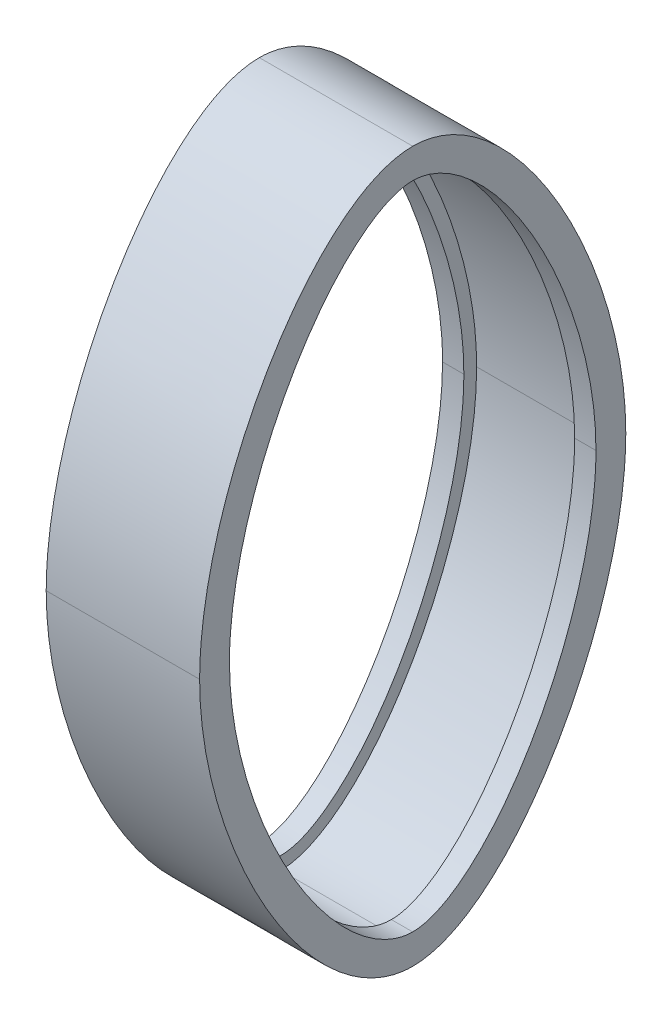
SolidWorks part; units mm, degrees
ref_plane "Front Plane" through (0, 0, 0) normal (0, 0, 1) x (1, 0, 0)
ref_plane "Top Plane" through (0, 0, 0) normal (0, 1, 0) x (1, 0, 0)
ref_plane "Right Plane" through (0, 0, 0) normal (1, 0, 0) x (0, 0, -1)
sketch "Sketch2" plane through (104.3753, 0, 0) normal (1, 0, 0) x (0, 0, -1)
  spline S4 degree 3 poles (2895.0888, -3813.0913) (-3233.4359, 4602.8109) (1881.6451, -5143.077) (-1713.8813, 4640.5368) knots -4.029718 -4.029718 -4.029718 -4.029718 4.699415 4.699415 4.699415 4.699415 only from (-367.1142, -61.0996) to (-317.1142, -144.4329)
  spline S5 degree 3 poles (1079.6132, 4640.4286) (-2515.8324, -5142.9962) (2599.1757, 4602.762) (-3529.3003, -3813.0682) knots -3.699383 -3.699383 -3.699383 -3.699383 5.02971 5.02971 5.02971 5.02971 only from (-317.1142, -144.4329) to (-267.1142, -61.0996)
  spline S6 degree 3 poles (-3529.3171, 3690.8921) (2599.2076, -4725.0101) (-2515.8734, 5020.8778) (1079.653, -4762.736) knots -4.029718 -4.029718 -4.029718 -4.029718 4.699415 4.699415 4.699415 4.699415 only from (-267.1142, -61.0996) to (-317.1142, 22.2337)
  spline S7 degree 3 poles (-1713.8415, -4762.6278) (1881.6041, 5020.797) (-3233.404, -4724.9612) (2895.072, 3690.869) knots -3.699383 -3.699383 -3.699383 -3.699383 5.02971 5.02971 5.02971 5.02971 only from (-317.1142, 22.2337) to (-367.1142, -61.0996)
  spline S8 degree 3 poles (-367.1142, -61.0996) (-367.1142, -97.7663) (-340.4475, -144.4329) (-317.1142, -144.4329) knots 0 0 0 0 1 1 1 1
  spline S9 degree 3 poles (-317.1142, -144.4329) (-293.7808, -144.4329) (-267.1142, -97.7663) (-267.1142, -61.0996) knots 0 0 0 0 1 1 1 1
  spline S10 degree 3 poles (-267.1142, -61.0996) (-267.1142, -24.4329) (-293.7808, 22.2337) (-317.1142, 22.2337) knots 0 0 0 0 1 1 1 1
  spline S11 degree 3 poles (-317.1142, 22.2337) (-340.4475, 22.2337) (-367.1142, -24.4329) (-367.1142, -61.0996) knots 0 0 0 0 1 1 1 1
  dimension "D1" = 0
extrude "Boss-Extrude1" add sketch "Sketch2" along normal offset from surface (18 mm away) 3
sketch "Sketch4" plane through (104.3753, 0, 0) normal (1, 0, 0) x (0, 0, -1)
  spline S8 degree 3 poles (3475.1569, 1041.7378) (-138.7623, 209.0275) (-368.8408, 47.3489) (-359.7286, -68.8551) (-359.5092, -70.7695) (-358.6746, -76.4779) (-357.8851, -80.2373) (-355.9167, -87.6789) (-354.7367, -91.3621) (-352.0035, -98.6494) (-350.4708, -102.1996) (-347.0714, -109.1118) (-345.2056, -112.4743) (-342.112, -117.3521) (-341.0312, -118.9501) (-339.3223, -121.2977) (-338.738, -122.072) (-337.5366, -123.6021) (-336.9186, -124.3591) (-335.0156, -126.5904) (-333.688, -128.0198) (-331.5805, -130.0493) (-330.8585, -130.7065) (-329.3674, -131.9744) (-328.6017, -132.5822) (-327.0312, -133.7267) (-326.2253, -134.2647) (-324.561, -135.2541) (-323.7028, -135.7058) (-321.9148, -136.4905) (-320.9764, -136.8252) (-279.2738, -147.1153) (-205.8613, 18.7108) (533.2817, 3769.6236) knots -3.641992 -3.641992 -3.641992 -3.641992 0.0625 0.0625 0.125 0.125 0.25 0.25 0.375 0.375 0.5 0.5 0.625 0.625 0.6875 0.6875 0.71875 0.71875 0.75 0.75 0.8125 0.8125 0.84375 0.84375 0.875 0.875 0.90625 0.90625 0.9375 0.9375 0.96875 0.96875 2.308967 2.308967 2.308967 2.308967 only from (-360.1142, -61.0996) to (-317.1142, -137.4329)
  spline S9 degree 3 poles (-1217.2008, 3758.4213) (-429.1845, 15.0336) (-354.5726, -146.9888) (-313.7401, -136.946) (-313.2721, -136.8057) (-312.3445, -136.4837) (-311.8854, -136.3021) (-310.5409, -135.7136) (-309.6796, -135.261) (-308.008, -134.2681) (-307.1978, -133.7274) (-306.0131, -132.8637) (-305.6226, -132.5664) (-304.8554, -131.9593) (-304.4785, -131.6495) (-303.3659, -130.7029) (-302.6481, -130.0495) (-300.554, -128.0334) (-299.2364, -126.6159) (-296.7196, -123.6695) (-295.5211, -122.1402) (-293.2233, -118.9884) (-292.1358, -117.3818) (-289.028, -112.4848) (-287.1605, -109.1182) (-283.7648, -102.2154) (-282.2378, -98.6788) (-280.1982, -93.2485) (-279.56, -91.4156) (-278.374, -87.7133) (-277.8294, -85.8538) (-276.3454, -80.2495) (-275.5537, -76.4791) (-274.7182, -70.7628) (-274.4989, -68.8472) (-265.2952, 48.66) (-501.3892, 206.5565) (-4134.1122, 950.7728) knots -1.302809 -1.302809 -1.302809 -1.302809 0.03125 0.03125 0.046875 0.046875 0.0625 0.0625 0.09375 0.09375 0.125 0.125 0.140625 0.140625 0.15625 0.15625 0.1875 0.1875 0.25 0.25 0.3125 0.3125 0.375 0.375 0.5 0.5 0.625 0.625 0.6875 0.6875 0.75 0.75 0.875 0.875 0.9375 0.9375 4.685331 4.685331 4.685331 4.685331 only from (-317.1142, -137.4329) to (-274.1142, -61.0996)
  spline S10 degree 3 poles (-4109.3852, -1163.937) (-495.466, -331.2267) (-265.3875, -169.5481) (-274.4997, -53.3441) (-274.7191, -51.4297) (-275.5537, -45.7213) (-276.3432, -41.9619) (-278.3116, -34.5203) (-279.4916, -30.8371) (-282.2248, -23.5498) (-283.7575, -19.9996) (-287.1569, -13.0874) (-289.0227, -9.7249) (-292.1163, -4.8471) (-293.1971, -3.2491) (-294.906, -0.9015) (-295.4903, -0.1272) (-296.6917, 1.4029) (-297.3097, 2.1599) (-299.2127, 4.3912) (-300.5403, 5.8206) (-302.6478, 7.8501) (-303.3698, 8.5073) (-304.8609, 9.7752) (-305.6266, 10.383) (-307.1971, 11.5275) (-308.003, 12.0655) (-309.6673, 13.0549) (-310.5255, 13.5066) (-312.3135, 14.2913) (-313.252, 14.626) (-354.9545, 24.9161) (-428.367, -140.91) (-1167.51, -3891.8228) knots -3.641992 -3.641992 -3.641992 -3.641992 0.0625 0.0625 0.125 0.125 0.25 0.25 0.375 0.375 0.5 0.5 0.625 0.625 0.6875 0.6875 0.71875 0.71875 0.75 0.75 0.8125 0.8125 0.84375 0.84375 0.875 0.875 0.90625 0.90625 0.9375 0.9375 0.96875 0.96875 2.308967 2.308967 2.308967 2.308967 only from (-274.1142, -61.0996) to (-317.1142, 15.2337)
  spline S11 degree 3 poles (582.9725, -3880.6205) (-205.0438, -137.2328) (-279.6557, 24.7896) (-320.4882, 14.7468) (-320.9562, 14.6065) (-321.8838, 14.2845) (-322.3429, 14.1029) (-323.6874, 13.5144) (-324.5487, 13.0618) (-326.2204, 12.0689) (-327.0305, 11.5282) (-328.2152, 10.6645) (-328.6057, 10.3672) (-329.3729, 9.7601) (-329.7498, 9.4503) (-330.8624, 8.5037) (-331.5802, 7.8503) (-333.6743, 5.8342) (-334.992, 4.4167) (-337.5087, 1.4703) (-338.7073, -0.059) (-341.005, -3.2108) (-342.0925, -4.8174) (-345.2003, -9.7144) (-347.0678, -13.081) (-350.4635, -19.9838) (-351.9905, -23.5204) (-354.0301, -28.9507) (-354.6684, -30.7836) (-355.8543, -34.4859) (-356.399, -36.3454) (-357.8829, -41.9497) (-358.6746, -45.7201) (-359.5101, -51.4364) (-359.7294, -53.352) (-368.9331, -170.8592) (-132.8391, -328.7557) (3499.8839, -1072.972) knots -1.302809 -1.302809 -1.302809 -1.302809 0.03125 0.03125 0.046875 0.046875 0.0625 0.0625 0.09375 0.09375 0.125 0.125 0.140625 0.140625 0.15625 0.15625 0.1875 0.1875 0.25 0.25 0.3125 0.3125 0.375 0.375 0.5 0.5 0.625 0.625 0.6875 0.6875 0.75 0.75 0.875 0.875 0.9375 0.9375 4.685331 4.685331 4.685331 4.685331 only from (-317.1142, 15.2337) to (-360.1142, -61.0996)
  spline S12 degree 3 poles (-360.1142, -61.0996) (-360.1142, -63.0576) (-360.031, -64.9991) (-359.7286, -68.8551) (-359.5092, -70.7695) (-358.6746, -76.4779) (-357.8851, -80.2373) (-355.9167, -87.6789) (-354.7367, -91.3621) (-352.0035, -98.6494) (-350.4708, -102.1996) (-347.0714, -109.1118) (-345.2056, -112.4743) (-342.112, -117.3521) (-341.0312, -118.9501) (-339.3223, -121.2977) (-338.738, -122.072) (-337.5366, -123.6021) (-336.9186, -124.3591) (-335.0156, -126.5904) (-333.688, -128.0198) (-331.5805, -130.0493) (-330.8585, -130.7065) (-329.3674, -131.9744) (-328.6017, -132.5822) (-327.0312, -133.7267) (-326.2253, -134.2647) (-324.561, -135.2541) (-323.7028, -135.7058) (-321.9148, -136.4905) (-320.9764, -136.8252) (-319.0759, -137.2941) (-318.1079, -137.4329) (-317.1142, -137.4329) knots 0 0 0 0 0.0625 0.0625 0.125 0.125 0.25 0.25 0.375 0.375 0.5 0.5 0.625 0.625 0.6875 0.6875 0.71875 0.71875 0.75 0.75 0.8125 0.8125 0.84375 0.84375 0.875 0.875 0.90625 0.90625 0.9375 0.9375 0.96875 0.96875 1 1 1 1
  spline S13 degree 3 poles (-317.1142, -137.4329) (-316.1224, -137.4329) (-315.1582, -137.2948) (-313.7401, -136.946) (-313.2721, -136.8057) (-312.3445, -136.4837) (-311.8854, -136.3021) (-310.5409, -135.7136) (-309.6796, -135.261) (-308.008, -134.2681) (-307.1978, -133.7274) (-306.0131, -132.8637) (-305.6226, -132.5664) (-304.8554, -131.9593) (-304.4785, -131.6495) (-303.3659, -130.7029) (-302.6481, -130.0495) (-300.554, -128.0334) (-299.2364, -126.6159) (-296.7196, -123.6695) (-295.5211, -122.1402) (-293.2233, -118.9884) (-292.1358, -117.3818) (-289.028, -112.4848) (-287.1605, -109.1182) (-283.7648, -102.2154) (-282.2378, -98.6788) (-280.1982, -93.2485) (-279.56, -91.4156) (-278.374, -87.7133) (-277.8294, -85.8538) (-276.3454, -80.2495) (-275.5537, -76.4791) (-274.7182, -70.7628) (-274.4989, -68.8472) (-274.1969, -64.9923) (-274.1142, -63.0531) (-274.1142, -61.0996) knots 0 0 0 0 0.03125 0.03125 0.046875 0.046875 0.0625 0.0625 0.09375 0.09375 0.125 0.125 0.140625 0.140625 0.15625 0.15625 0.1875 0.1875 0.25 0.25 0.3125 0.3125 0.375 0.375 0.5 0.5 0.625 0.625 0.6875 0.6875 0.75 0.75 0.875 0.875 0.9375 0.9375 1 1 1 1
  spline S14 degree 3 poles (-274.1142, -61.0996) (-274.1142, -59.1416) (-274.1973, -57.2001) (-274.4997, -53.3441) (-274.7191, -51.4297) (-275.5537, -45.7213) (-276.3432, -41.9619) (-278.3116, -34.5203) (-279.4916, -30.8371) (-282.2248, -23.5498) (-283.7575, -19.9996) (-287.1569, -13.0874) (-289.0227, -9.7249) (-292.1163, -4.8471) (-293.1971, -3.2491) (-294.906, -0.9015) (-295.4903, -0.1272) (-296.6917, 1.4029) (-297.3097, 2.1599) (-299.2127, 4.3912) (-300.5403, 5.8206) (-302.6478, 7.8501) (-303.3698, 8.5073) (-304.8609, 9.7752) (-305.6266, 10.383) (-307.1971, 11.5275) (-308.003, 12.0655) (-309.6673, 13.0549) (-310.5255, 13.5066) (-312.3135, 14.2913) (-313.252, 14.626) (-315.1524, 15.0949) (-316.1204, 15.2337) (-317.1142, 15.2337) knots 0 0 0 0 0.0625 0.0625 0.125 0.125 0.25 0.25 0.375 0.375 0.5 0.5 0.625 0.625 0.6875 0.6875 0.71875 0.71875 0.75 0.75 0.8125 0.8125 0.84375 0.84375 0.875 0.875 0.90625 0.90625 0.9375 0.9375 0.96875 0.96875 1 1 1 1
  spline S15 degree 3 poles (-317.1142, 15.2337) (-318.1059, 15.2337) (-319.0701, 15.0956) (-320.4882, 14.7468) (-320.9562, 14.6065) (-321.8838, 14.2845) (-322.3429, 14.1029) (-323.6874, 13.5144) (-324.5487, 13.0618) (-326.2204, 12.0689) (-327.0305, 11.5282) (-328.2152, 10.6645) (-328.6057, 10.3672) (-329.3729, 9.7601) (-329.7498, 9.4503) (-330.8624, 8.5037) (-331.5802, 7.8503) (-333.6743, 5.8342) (-334.992, 4.4167) (-337.5087, 1.4703) (-338.7073, -0.059) (-341.005, -3.2108) (-342.0925, -4.8174) (-345.2003, -9.7144) (-347.0678, -13.081) (-350.4635, -19.9838) (-351.9905, -23.5204) (-354.0301, -28.9507) (-354.6684, -30.7836) (-355.8543, -34.4859) (-356.399, -36.3454) (-357.8829, -41.9497) (-358.6746, -45.7201) (-359.5101, -51.4364) (-359.7294, -53.352) (-360.0314, -57.2069) (-360.1142, -59.1461) (-360.1142, -61.0996) knots 0 0 0 0 0.03125 0.03125 0.046875 0.046875 0.0625 0.0625 0.09375 0.09375 0.125 0.125 0.140625 0.140625 0.15625 0.15625 0.1875 0.1875 0.25 0.25 0.3125 0.3125 0.375 0.375 0.5 0.5 0.625 0.625 0.6875 0.6875 0.75 0.75 0.875 0.875 0.9375 0.9375 1 1 1 1
  dimension "D1" = 7
extrude "Cut-Extrude2" cut sketch "Sketch4" along normal up to surface (5 mm away)
sketch "Sketch6" plane through (109.3753, 0, 0) normal (-1, 0, 0) x (0, 0, 1)
  spline S0 degree 3 poles (-321.1313, 2789.2693) (198.4498, 26.5186) (275.2056, -149.6018) (320.6862, -139.9947) (321.185, -139.865) (322.1755, -139.5638) (322.6663, -139.3923) (324.1036, -138.8318) (325.025, -138.3949) (326.8125, -137.4263) (327.6785, -136.8944) (329.3659, -135.7541) (330.1872, -135.1456) (331.7925, -133.8643) (332.5735, -133.1936) (334.8449, -131.121) (336.2725, -129.653) (338.3162, -127.3538) (338.982, -126.5694) (340.2767, -124.9799) (340.9056, -124.1749) (342.7435, -121.7322) (343.9036, -120.067) (347.2201, -114.9794) (349.2149, -111.466) (352.845, -104.2367) (354.4792, -100.5203) (356.2993, -95.7495) (356.6518, -94.7894) (357.3306, -92.8666) (357.6572, -91.9027) (358.5988, -89.0034) (359.1755, -87.0605) (360.7473, -81.2004) (361.5866, -77.2525) (362.4729, -71.2571) (362.7057, -69.2462) (371.3059, 39.4354) (179.1648, 185.7037) (-2495.4618, 822.2274) knots -1.366399 -1.366399 -1.366399 -1.366399 0.03125 0.03125 0.046875 0.046875 0.0625 0.0625 0.09375 0.09375 0.125 0.125 0.15625 0.15625 0.1875 0.1875 0.25 0.25 0.28125 0.28125 0.3125 0.3125 0.375 0.375 0.5 0.5 0.625 0.625 0.65625 0.65625 0.6875 0.6875 0.75 0.75 0.875 0.875 0.9375 0.9375 4.22908 4.22908 4.22908 4.22908 only from (317.1142, -140.4329) to (363.1142, -61.0996) construction
  spline S1 degree 3 poles (3174.7475, 657.9394) (467.5752, 181.1133) (262.6885, 42.5166) (271.522, -69.2411) (271.7553, -71.2587) (272.3498, -75.2766) (272.7111, -77.2769) (273.3402, -80.2656) (273.5645, -81.2599) (274.0413, -83.2445) (274.2942, -84.2359) (275.6205, -89.1606) (276.8819, -93.0129) (279.7673, -100.5595) (281.3913, -104.2538) (285.0192, -111.4765) (287.0216, -115.0057) (290.3778, -120.1456) (291.5472, -121.8191) (293.9974, -125.0674) (295.2788, -126.6436) (297.9799, -129.6777) (299.399, -131.1362) (301.6674, -133.2046) (302.4498, -133.876) (304.053, -135.1546) (304.8745, -135.7628) (306.5652, -136.9041) (307.4344, -137.4375) (308.7833, -138.1667) (309.2405, -138.3979) (310.1723, -138.8329) (310.6489, -139.0374) (312.0891, -139.5952) (313.065, -139.8949) (357.3476, -149.2038) (438.017, 11.6892) (1087.1312, 2757.5084) knots -3.320085 -3.320085 -3.320085 -3.320085 0.0625 0.0625 0.125 0.125 0.1875 0.1875 0.21875 0.21875 0.25 0.25 0.375 0.375 0.5 0.5 0.625 0.625 0.6875 0.6875 0.75 0.75 0.8125 0.8125 0.84375 0.84375 0.875 0.875 0.90625 0.90625 0.921875 0.921875 0.9375 0.9375 0.96875 0.96875 2.327131 2.327131 2.327131 2.327131 only from (271.1142, -61.0996) to (317.1142, -140.4329) construction
  spline S2 degree 3 poles (955.3596, -2911.4685) (435.7785, -148.7178) (359.0227, 27.4026) (313.5421, 17.7955) (313.0433, 17.6658) (312.0528, 17.3646) (311.562, 17.1931) (310.1247, 16.6326) (309.2033, 16.1957) (307.4158, 15.2271) (306.5499, 14.6952) (304.8624, 13.5549) (304.0411, 12.9464) (302.4358, 11.6651) (301.6548, 10.9944) (299.3834, 8.9218) (297.9558, 7.4538) (295.9122, 5.1546) (295.2463, 4.3702) (293.9516, 2.7807) (293.3227, 1.9757) (291.4848, -0.467) (290.3247, -2.1322) (287.0082, -7.2198) (285.0134, -10.7332) (281.3833, -17.9625) (279.7491, -21.6789) (277.929, -26.4497) (277.5765, -27.4098) (276.8978, -29.3326) (276.5711, -30.2965) (275.6295, -33.1958) (275.0528, -35.1387) (273.481, -40.9988) (272.6417, -44.9467) (271.7554, -50.9421) (271.5226, -52.953) (262.9224, -161.6346) (455.0635, -307.9029) (3129.6901, -944.4266) knots -1.366399 -1.366399 -1.366399 -1.366399 0.03125 0.03125 0.046875 0.046875 0.0625 0.0625 0.09375 0.09375 0.125 0.125 0.15625 0.15625 0.1875 0.1875 0.25 0.25 0.28125 0.28125 0.3125 0.3125 0.375 0.375 0.5 0.5 0.625 0.625 0.65625 0.65625 0.6875 0.6875 0.75 0.75 0.875 0.875 0.9375 0.9375 4.22908 4.22908 4.22908 4.22908 only from (317.1142, 18.2337) to (271.1142, -61.0996) construction
  spline S3 degree 3 poles (-2540.5191, -780.1386) (166.6531, -303.3126) (371.5398, -164.7158) (362.7063, -52.9581) (362.473, -50.9405) (361.8785, -46.9226) (361.5172, -44.9223) (360.8881, -41.9336) (360.6638, -40.9394) (360.187, -38.9547) (359.9342, -37.9633) (358.6078, -33.0386) (357.3464, -29.1863) (354.461, -21.6397) (352.837, -17.9454) (349.2091, -10.7227) (347.2067, -7.1935) (343.8505, -2.0536) (342.6811, -0.3801) (340.2309, 2.8682) (338.9495, 4.4444) (336.2484, 7.4785) (334.8294, 8.937) (332.561, 11.0054) (331.7785, 11.6768) (330.1753, 12.9554) (329.3538, 13.5636) (327.6631, 14.7049) (326.794, 15.2383) (325.4451, 15.9675) (324.9878, 16.1987) (324.056, 16.6337) (323.5794, 16.8382) (322.1392, 17.396) (321.1633, 17.6957) (276.8807, 27.0046) (196.2113, -133.8884) (-452.9029, -2879.7076) knots -3.320085 -3.320085 -3.320085 -3.320085 0.0625 0.0625 0.125 0.125 0.1875 0.1875 0.21875 0.21875 0.25 0.25 0.375 0.375 0.5 0.5 0.625 0.625 0.6875 0.6875 0.75 0.75 0.8125 0.8125 0.84375 0.84375 0.875 0.875 0.90625 0.90625 0.921875 0.921875 0.9375 0.9375 0.96875 0.96875 2.327131 2.327131 2.327131 2.327131 only from (363.1142, -61.0996) to (317.1142, 18.2337) construction
  spline S4 degree 3 poles (317.1142, -140.4329) (318.1562, -140.4329) (319.1777, -140.3133) (320.6862, -139.9947) (321.185, -139.865) (322.1755, -139.5638) (322.6663, -139.3923) (324.1036, -138.8318) (325.025, -138.3949) (326.8125, -137.4263) (327.6785, -136.8944) (329.3659, -135.7541) (330.1872, -135.1456) (331.7925, -133.8643) (332.5735, -133.1936) (334.8449, -131.121) (336.2725, -129.653) (338.3162, -127.3538) (338.982, -126.5694) (340.2767, -124.9799) (340.9056, -124.1749) (342.7435, -121.7322) (343.9036, -120.067) (347.2201, -114.9794) (349.2149, -111.466) (352.845, -104.2367) (354.4792, -100.5203) (356.2993, -95.7495) (356.6518, -94.7894) (357.3306, -92.8666) (357.6572, -91.9027) (358.5988, -89.0034) (359.1755, -87.0605) (360.7473, -81.2004) (361.5866, -77.2525) (362.4729, -71.2571) (362.7057, -69.2462) (363.0262, -65.1959) (363.1142, -63.1564) (363.1142, -61.0996) knots 0 0 0 0 0.03125 0.03125 0.046875 0.046875 0.0625 0.0625 0.09375 0.09375 0.125 0.125 0.15625 0.15625 0.1875 0.1875 0.25 0.25 0.28125 0.28125 0.3125 0.3125 0.375 0.375 0.5 0.5 0.625 0.625 0.65625 0.65625 0.6875 0.6875 0.75 0.75 0.875 0.875 0.9375 0.9375 1 1 1 1
  spline S5 degree 3 poles (271.1142, -61.0996) (271.1142, -63.1487) (271.2015, -65.1861) (271.522, -69.2411) (271.7553, -71.2587) (272.3498, -75.2766) (272.7111, -77.2769) (273.3402, -80.2656) (273.5645, -81.2599) (274.0413, -83.2445) (274.2942, -84.2359) (275.6205, -89.1606) (276.8819, -93.0129) (279.7673, -100.5595) (281.3913, -104.2538) (285.0192, -111.4765) (287.0216, -115.0057) (290.3778, -120.1456) (291.5472, -121.8191) (293.9974, -125.0674) (295.2788, -126.6436) (297.9799, -129.6777) (299.399, -131.1362) (301.6674, -133.2046) (302.4498, -133.876) (304.053, -135.1546) (304.8745, -135.7628) (306.5652, -136.9041) (307.4344, -137.4375) (308.7833, -138.1667) (309.2405, -138.3979) (310.1723, -138.8329) (310.6489, -139.0374) (312.0891, -139.5952) (313.065, -139.8949) (315.0567, -140.3136) (316.0723, -140.4329) (317.1142, -140.4329) knots 0 0 0 0 0.0625 0.0625 0.125 0.125 0.1875 0.1875 0.21875 0.21875 0.25 0.25 0.375 0.375 0.5 0.5 0.625 0.625 0.6875 0.6875 0.75 0.75 0.8125 0.8125 0.84375 0.84375 0.875 0.875 0.90625 0.90625 0.921875 0.921875 0.9375 0.9375 0.96875 0.96875 1 1 1 1
  spline S6 degree 3 poles (317.1142, 18.2337) (316.0721, 18.2337) (315.0506, 18.1141) (313.5421, 17.7955) (313.0433, 17.6658) (312.0528, 17.3646) (311.562, 17.1931) (310.1247, 16.6326) (309.2033, 16.1957) (307.4158, 15.2271) (306.5499, 14.6952) (304.8624, 13.5549) (304.0411, 12.9464) (302.4358, 11.6651) (301.6548, 10.9944) (299.3834, 8.9218) (297.9558, 7.4538) (295.9122, 5.1546) (295.2463, 4.3702) (293.9516, 2.7807) (293.3227, 1.9757) (291.4848, -0.467) (290.3247, -2.1322) (287.0082, -7.2198) (285.0134, -10.7332) (281.3833, -17.9625) (279.7491, -21.6789) (277.929, -26.4497) (277.5765, -27.4098) (276.8978, -29.3326) (276.5711, -30.2965) (275.6295, -33.1958) (275.0528, -35.1387) (273.481, -40.9988) (272.6417, -44.9467) (271.7554, -50.9421) (271.5226, -52.953) (271.2021, -57.0033) (271.1142, -59.0428) (271.1142, -61.0996) knots 0 0 0 0 0.03125 0.03125 0.046875 0.046875 0.0625 0.0625 0.09375 0.09375 0.125 0.125 0.15625 0.15625 0.1875 0.1875 0.25 0.25 0.28125 0.28125 0.3125 0.3125 0.375 0.375 0.5 0.5 0.625 0.625 0.65625 0.65625 0.6875 0.6875 0.75 0.75 0.875 0.875 0.9375 0.9375 1 1 1 1
  spline S7 degree 3 poles (363.1142, -61.0996) (363.1142, -59.0505) (363.0268, -57.0131) (362.7063, -52.9581) (362.473, -50.9405) (361.8785, -46.9226) (361.5172, -44.9223) (360.8881, -41.9336) (360.6638, -40.9394) (360.187, -38.9547) (359.9342, -37.9633) (358.6078, -33.0386) (357.3464, -29.1863) (354.461, -21.6397) (352.837, -17.9454) (349.2091, -10.7227) (347.2067, -7.1935) (343.8505, -2.0536) (342.6811, -0.3801) (340.2309, 2.8682) (338.9495, 4.4444) (336.2484, 7.4785) (334.8294, 8.937) (332.561, 11.0054) (331.7785, 11.6768) (330.1753, 12.9554) (329.3538, 13.5636) (327.6631, 14.7049) (326.794, 15.2383) (325.4451, 15.9675) (324.9878, 16.1987) (324.056, 16.6337) (323.5794, 16.8382) (322.1392, 17.396) (321.1633, 17.6957) (319.1716, 18.1144) (318.156, 18.2337) (317.1142, 18.2337) knots 0 0 0 0 0.0625 0.0625 0.125 0.125 0.1875 0.1875 0.21875 0.21875 0.25 0.25 0.375 0.375 0.5 0.5 0.625 0.625 0.6875 0.6875 0.75 0.75 0.8125 0.8125 0.84375 0.84375 0.875 0.875 0.90625 0.90625 0.921875 0.921875 0.9375 0.9375 0.96875 0.96875 1 1 1 1
extrude "Cut-Extrude3" cut sketch "Sketch6" against normal through all
ref_plane "Plane1" through (122.3753, 0, 0) normal (1, 0, 0) x (0, 0, -1)
mirror "Mirror1" about plane through (122.3753, 0, 0) normal (1, 0, 0) of bodies 103
ref_plane "Plane2" through (0, 0, 317.1142) normal (0, 0, 1) x (1, 0, 0)
